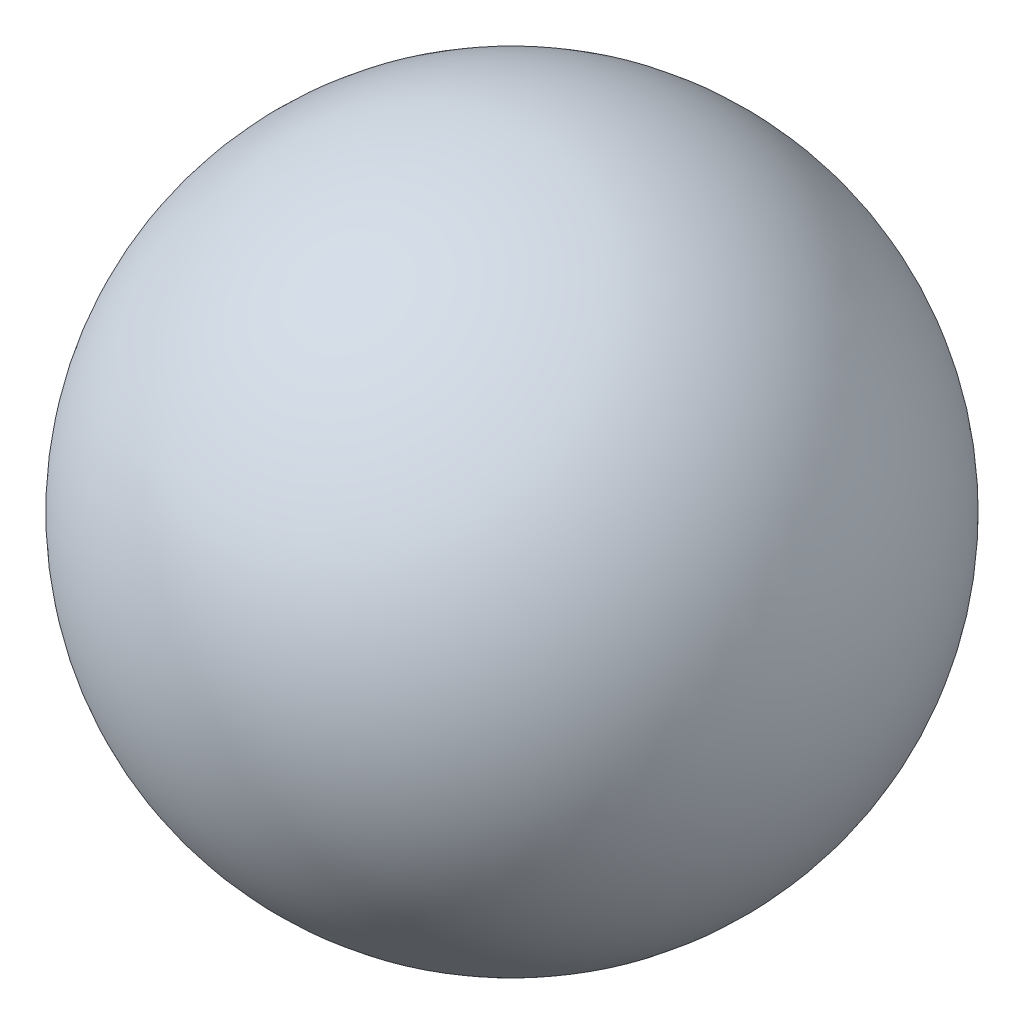
SolidWorks part; units mm, degrees
ref_plane "Front Plane" through (0, 0, 0) normal (0, 0, 1) x (1, 0, 0)
ref_plane "Top Plane" through (0, 0, 0) normal (0, 1, 0) x (1, 0, 0)
ref_plane "Right Plane" through (0, 0, 0) normal (1, 0, 0) x (0, 0, -1)
sketch "Sketch2" plane through (0, 0, 0) normal (0, 0, 1) x (1, 0, 0)
  line L0 (0, -7.1567) -> (0, 7.1567) construction
  line L1 (0, 3.9687) -> (0, -3.9687)
  arc A0 (0, 3.9687) -> (0, -3.9687) centre (0, 0) ccw
  point P4 (0, 0)
  dimension "D1" = 7.9375
revolve "Revolve1" add sketch "Sketch2" angle 360 about L0
